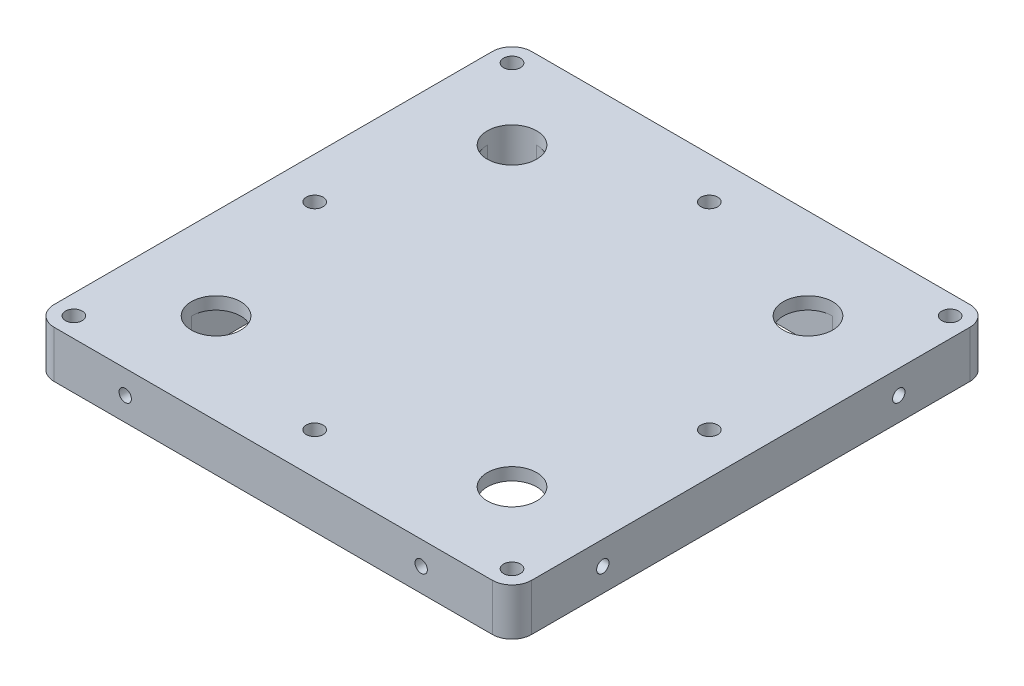
SolidWorks part; units mm, degrees
material "6061-T6 (SS)"
ref_plane "Front Plane" through (0, 0, 0) normal (0, 0, 1) x (1, 0, 0)
ref_plane "Top Plane" through (0, 0, 0) normal (0, 1, 0) x (1, 0, 0)
ref_plane "Right Plane" through (0, 0, 0) normal (1, 0, 0) x (0, 0, -1)
sketch "Sketch1" plane through (0, 0, 0) normal (0, 1, 0) x (1, 0, 0)
  line L1 (48.4125, -48.4125) -> (-48.4125, -48.4125)
  line L2 (48.4125, -48.4125) -> (48.4125, 48.4125)
  line L3 (48.4125, 48.4125) -> (-48.4125, 48.4125)
  line L4 (-48.4125, -48.4125) -> (-48.4125, 48.4125)
  line L5 (48.4125, -48.4125) -> (-48.4125, 48.4125) construction
  line L6 (48.4125, 48.4125) -> (-48.4125, -48.4125) construction
  point P0 (0, 0)
  dimension "D1" = 96.825
extrude "Boss-Extrude1" add sketch "Sketch1" along normal mid plane 9.525
fillet "Fillet1" radius 4 4 edges at (-48.4125, 0, -48.4125) (48.4125, 0, -48.4125) (48.4125, 0, 48.4125) (-48.4125, 0, 48.4125)
hole_wizard "M3x0.5 Tapped Hole1" positions "Sketch4" profile "Sketch3" tap size "M3x0.5" standard "ANSI Metric"
sketch "Sketch4" plane through (-48.4125, 0, 0) normal (-1, 0, 0) x (0, 0, 1)
  point P0 (-30, 0)
  point P2 (30, 0)
  dimension "D1" = 30
  dimension "D2" = 30
sketch "Sketch3" plane through (-48.4125, 0, -30) normal (0, 1, 0) x (0, 0, 1)
  line L0 (0, 0) -> (0, 10.7511)
  line L1 (0, 10.7511) -> (1.25, 10)
  line L2 (1.25, 10) -> (1.25, 0)
  line L5 (1.25, 0) -> (0, 0)
  line L10 (0, 10.7511) -> (-1.25, 10) construction
  line L11 (0, -6.35) -> (0, 107.95) construction
  dimension "Tap Drill Dia." = 2.5
  dimension "Tap Drill Depth" = 10
  dimension "Drill Angle" = 118
hole_wizard "M3x0.5 Tapped Hole2" positions "Sketch7" profile "Sketch6" tap size "M3x0.5" standard "ANSI Metric"
sketch "Sketch7" plane through (0, 0, -48.4125) normal (0, 0, -1) x (-1, 0, 0)
  point P0 (-30, 0)
  point P2 (30, 0)
  dimension "D1" = 30
  dimension "D2" = 30
sketch "Sketch6" plane through (30, 0, -48.4125) normal (1, 0, 0) x (0, 1, 0)
  line L0 (0, 0) -> (0, 10.7511)
  line L1 (0, 10.7511) -> (1.25, 10)
  line L2 (1.25, 10) -> (1.25, 0)
  line L5 (1.25, 0) -> (0, 0)
  line L10 (0, 10.7511) -> (-1.25, 10) construction
  line L11 (0, -6.35) -> (0, 107.95) construction
  dimension "Tap Drill Dia." = 2.5
  dimension "Tap Drill Depth" = 10
  dimension "Drill Angle" = 118
hole_wizard "M3 Clearance Hole1" positions "Sketch10" profile "Sketch9" hole size "M3" standard "ANSI Metric" end condition through all
sketch "Sketch10" plane through (0, 4.7625, 0) normal (0, 1, 0) x (1, 0, 0)
  arc A0 (-48.4125, -44.4125) -> (-44.4125, -48.4125) centre (-44.4125, -44.4125) ccw construction
  arc A1 (-44.4125, 48.4125) -> (-48.4125, 44.4125) centre (-44.4125, 44.4125) ccw construction
  arc A2 (48.4125, 44.4125) -> (44.4125, 48.4125) centre (44.4125, 44.4125) ccw construction
  arc A3 (44.4125, -48.4125) -> (48.4125, -44.4125) centre (44.4125, -44.4125) ccw construction
  point P0 (-44.4125, 44.4125)
  point P2 (44.4125, 44.4125)
  point P4 (44.4125, -44.4125)
  point P6 (-44.4125, -44.4125)
sketch "Sketch9" plane through (-44.4125, 4.7625, -44.4125) normal (1, 0, 0) x (0, 0, 1)
  line L0 (0, 0) -> (0, 9.525)
  line L1 (0, 9.525) -> (1.7, 9.525)
  line L2 (1.7, 9.525) -> (1.7, 0)
  line L5 (1.7, 0) -> (0, 0)
  line L11 (0, -6.35) -> (0, 107.95) construction
  dimension "Thru Hole Dia." = 3.4
  dimension "Thru Hole Depth" = 9.525
hole_wizard "M3x0.5 Tapped Hole3" positions "Sketch13" profile "Sketch12" tap size "M3x0.5" standard "ANSI Metric"
sketch "Sketch13" plane through (48.4125, 0, 0) normal (1, 0, 0) x (0, 0, -1)
  point P0 (-30, 0)
  point P2 (30, 0)
  dimension "D1" = 30
  dimension "D2" = 30
sketch "Sketch12" plane through (48.4125, 0, 30) normal (0, 1, 0) x (0, 0, -1)
  line L0 (0, 0) -> (0, 10.7511)
  line L1 (0, 10.7511) -> (1.25, 10)
  line L2 (1.25, 10) -> (1.25, 0)
  line L5 (1.25, 0) -> (0, 0)
  line L10 (0, 10.7511) -> (-1.25, 10) construction
  line L11 (0, -6.35) -> (0, 107.95) construction
  dimension "Tap Drill Dia." = 2.5
  dimension "Tap Drill Depth" = 10
  dimension "Drill Angle" = 118
hole_wizard "M3x0.5 Tapped Hole4" positions "Sketch16" profile "Sketch15" tap size "M3x0.5" standard "ANSI Metric"
sketch "Sketch16" plane through (0, 0, 48.4125) normal (0, 0, 1) x (1, 0, 0)
  point P0 (-30, 0)
  point P2 (30, 0)
  dimension "D1" = 30
  dimension "D2" = 30
sketch "Sketch15" plane through (-30, 0, 48.4125) normal (1, 0, 0) x (0, -1, 0)
  line L0 (0, 0) -> (0, 10.7511)
  line L1 (0, 10.7511) -> (1.25, 10)
  line L2 (1.25, 10) -> (1.25, 0)
  line L5 (1.25, 0) -> (0, 0)
  line L10 (0, 10.7511) -> (-1.25, 10) construction
  line L11 (0, -6.35) -> (0, 107.95) construction
  dimension "Tap Drill Dia." = 2.5
  dimension "Tap Drill Depth" = 10
  dimension "Drill Angle" = 118
hole_wizard "CSK for M3 SFHCS1" positions "Sketch19" profile "Sketch18" countersink size "M3" standard "ANSI Metric" end condition through all
sketch "Sketch19" plane through (0, -4.7625, 0) normal (0, -1, 0) x (-1, 0, 0)
  line L0 (0, 40) -> (0, -40) construction
  line L2 (-40, 0) -> (40, 0) construction
  point P0 (-40, 0)
  point P2 (0, 40)
  point P4 (40, 0)
  point P6 (0, -40)
  point P20 (0, 0)
  point P23 (0, 0)
  dimension "D1" = 40
  dimension "D2" = 40
sketch "Sketch18" plane through (40, -4.7625, 0) normal (1, 0, 0) x (0, 0, -1)
  line L0 (0, 0) -> (0, 9.525)
  line L1 (0, 9.525) -> (1.7, 9.525)
  line L2 (1.7, 9.525) -> (1.7, 1.66)
  line L3 (1.7, 1.66) -> (3.36, 0)
  line L5 (3.36, 0) -> (0, 0)
  line L6 (-1.7, 1.66) -> (-3.36, 0) construction
  line L11 (0, -6.35) -> (0, 107.95) construction
  dimension "Thru Hole Dia." = 3.4
  dimension "Thru Hole Depth" = 9.525
  dimension "Near C'Sink Dia." = 6.72
  dimension "Near C'Sink Angle" = 90
sketch "Sketch20" plane through (0, -4.7625, 0) normal (0, -1, 0) x (1, 0, 0)
  line L1 (30, -35) -> (-30, -35)
  line L2 (35, -30) -> (35, 30)
  line L3 (30, 35) -> (-30, 35)
  line L4 (-35, -30) -> (-35, 30)
  line L5 (35, -35) -> (-35, 35) construction
  line L6 (35, 35) -> (-35, -35) construction
  arc A0 (-30, -35) -> (-35, -30) centre (-30, -30) cw
  arc A1 (30, -35) -> (35, -30) centre (30, -30) ccw
  arc A2 (35, 30) -> (30, 35) centre (30, 30) ccw
  arc A3 (-30, 35) -> (-35, 30) centre (-30, 30) ccw
  point P0 (0, 0)
  dimension "D3" = 5
  dimension "D1" = 70
  dimension "D2" = 70
extrude "Cut-Extrude1" cut sketch "Sketch20" against normal blind 7
sketch "Sketch21" plane through (0, 2.2375, 0) normal (0, -1, 0) x (1, 0, 0)
  circle A0 centre (-30, 30) radius 5
  circle A1 centre (30, 30) radius 5
  circle A2 centre (30, -30) radius 5
  circle A3 centre (-30, -30) radius 5
  dimension "D1" = 10
  dimension "D2" = 10
  dimension "D3" = 10
  dimension "D4" = 10
extrude "Cut-Extrude2" cut sketch "Sketch21" against normal through all
